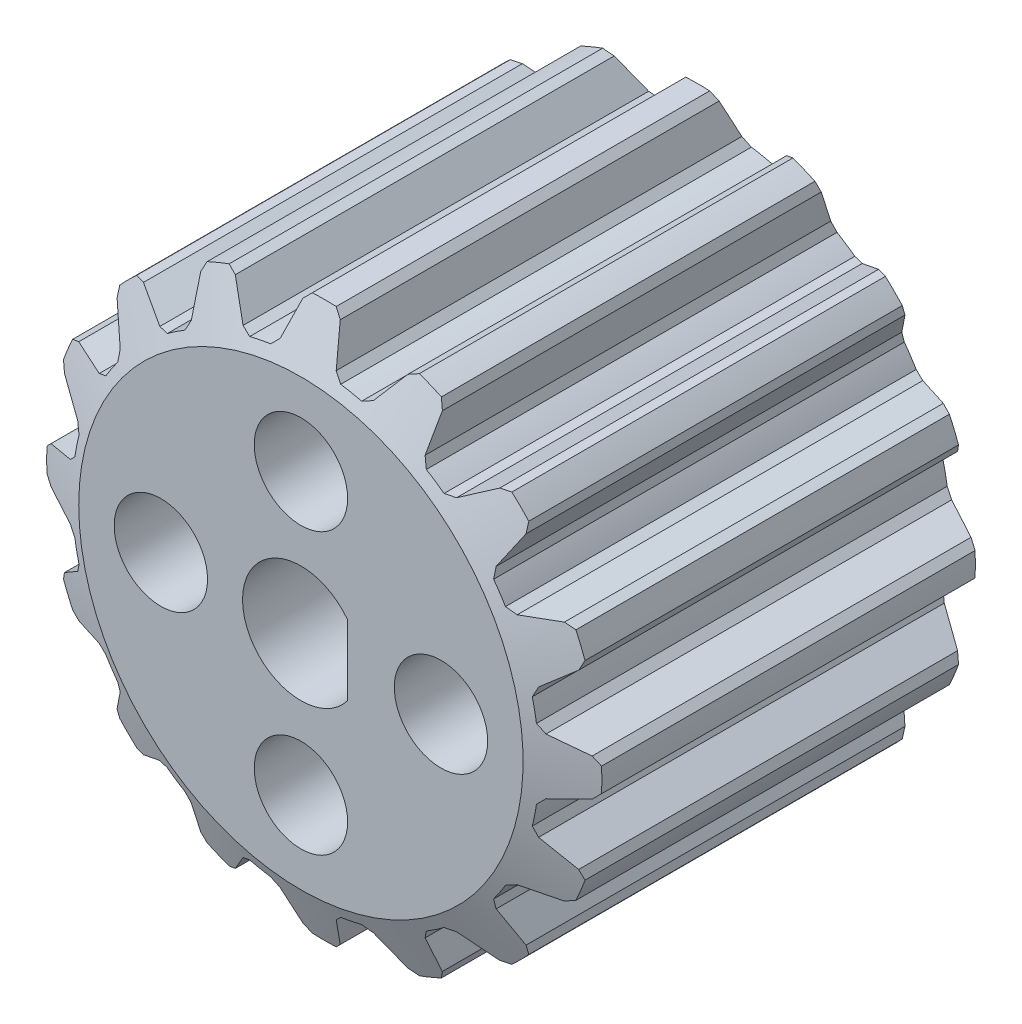
SolidWorks part; units mm, degrees
ref_plane "Front Plane" through (0, 0, 0) normal (0, 0, 1) x (1, 0, 0)
ref_plane "Top Plane" through (0, 0, 0) normal (0, 1, 0) x (1, 0, 0)
ref_plane "Right Plane" through (0, 0, 0) normal (1, 0, 0) x (0, 0, -1)
sketch "Sketch1" plane through (0, 0, 0) normal (0, 0, 1) x (1, 0, 0)
  line L0 (0, 0) -> (0, 16.6022) construction
  circle A0 centre (0, 0) radius 10
  circle A2 centre (0, 0) radius 12 construction
  point P3 (-1, 11.488)
  point P16 (-0.5, 11.9896)
  point P17 (0, 0)
  point P18 (0, 0)
  dimension "D1" = 20
  dimension "D8" = 24
extrude "Boss-Extrude1" add sketch "Sketch1" along normal blind 18 contours A0
sketch "Sketch2" plane through (0, 0, 18) normal (0, 0, 1) x (1, 0, 0)
  line L0 (0, 0) -> (0, 14.431) construction
  line L1 (-0.8, 11.5895) -> (-1.2, 10.1869)
  line L2 (1.5, 9.8869) -> (1.2, 10.1869)
  line L3 (-0.8, 11.5895) -> (-0.5, 11.8895)
  line L4 (-1.5, 9.8869) -> (-1.2, 10.1869)
  line L5 (0.8, 11.5895) -> (1.2, 10.1869)
  line L6 (0.8, 11.5895) -> (0.5, 11.8895)
  line L7 (-1.5, 9.8869) -> (-1.5, 9.5345)
  line L8 (1.5, 9.8869) -> (1.5, 9.5345)
  line L9 (-1.5, 9.5345) -> (1.5, 9.5345)
  arc A1 (0.5, 11.8895) -> (-0.5, 11.8895) centre (0, -74.9815) ccw
  circle A2 centre (0, 0) radius 11.9 construction
  point P1 (0, 0)
  point P15 (0, 0)
  dimension "D7" = 23.8
  dimension "D2" = 3
  dimension "D3" = 1
  dimension "D4" = 1.6
  dimension "D5" = 0.3
  dimension "D6" = 0.3
  dimension "D8" = 0.3
  dimension "D9" = 0.3
  dimension "D10" = 0.3
sketch3d "3DSketch2"
  line L0 (0, 11.8909, 18) -> (0, 11.8909, -2.0718)
  line L1 (0, 0, 18) -> (0, 14.431, 18) construction
  line L2 (0, 11.8909, 18) -> (11.5493, 11.8909, 18) construction
  arc A0 (0.5, 11.8895, 18) -> (-0.5, 11.8895, 18) centre (0, -74.9815, 18) ccw construction
  point P5 (0, -74.9815, 104.8724)
  dimension "D1" = 90
sweep "Sweep1" add profiles "Sketch2" path "3DSketch2"
pattern_circular "CirPattern1" count 16 over 360 about axis through (0, 0, 0) along (0, 0, 1) of "Sweep1"
sketch "Sketch4" plane through (0, 0, 18) normal (0, 0, 1) x (1, 0, 0)
  line L0 (-2.5, 0) -> (-2.5, 6.0434) construction
  line L1 (2, 1.5) -> (2, -1.5)
  arc A0 (2, 1.5) -> (2, -1.5) centre (0, 0) ccw
  dimension "D1" = 5
  dimension "D2" = 4.5
extrude "Cut-Extrude1" cut sketch "Sketch4" against normal blind 37
sketch "Sketch5" plane through (0, 0, 0) normal (1, 0, 0) x (0, 0, -1)
  line L0 (0, 0) -> (-28.0609, 0) construction
  line L1 (-17, 11.8895) -> (-18, 9.5177)
  line L2 (-18, 9.5177) -> (-22.1801, 9.5177)
  line L3 (-22.1801, 9.5177) -> (-22.1801, 15.2583)
  line L4 (-22.1801, 15.2583) -> (5.974, 15.2583)
  line L5 (5.974, 15.2583) -> (5.974, 9.5177)
  line L6 (5.974, 9.5177) -> (0, 9.5177)
  line L7 (0, 9.5177) -> (-1, 11.8895)
  line L8 (-1, 11.8895) -> (-17, 11.8895)
  line L10 (-18, 11.8895) -> (2.0718, 11.8895) construction
  line L12 (-9, 0) -> (-9, 27.6976) construction
  line L13 (-18, 2.7897) -> (-18, 3.696) construction
  point P11 (0, 0)
  point P19 (0, 0)
  point P22 (0, 0)
  point P23 (0, 0)
  dimension "D1" = 16
  dimension "D2" = 9
revolve "Cut-Revolve1" cut sketch "Sketch5" angle 360 about L0
sketch "Sketch6" plane through (0, 0, 18) normal (0, 0, 1) x (1, 0, 0)
  circle A0 centre (0, 0) radius 6 construction
  circle A2 centre (0, 6) radius 2
  circle A3 centre (6, 0) radius 2
  circle A4 centre (0, -6) radius 2
  circle A5 centre (-6, 0) radius 2
  dimension "D1" = 12
  dimension "D2" = 4
  dimension "D3" = 4
  dimension "D4" = 4
  dimension "D5" = 4
extrude "Cut-Extrude2" cut sketch "Sketch6" against normal blind 37
